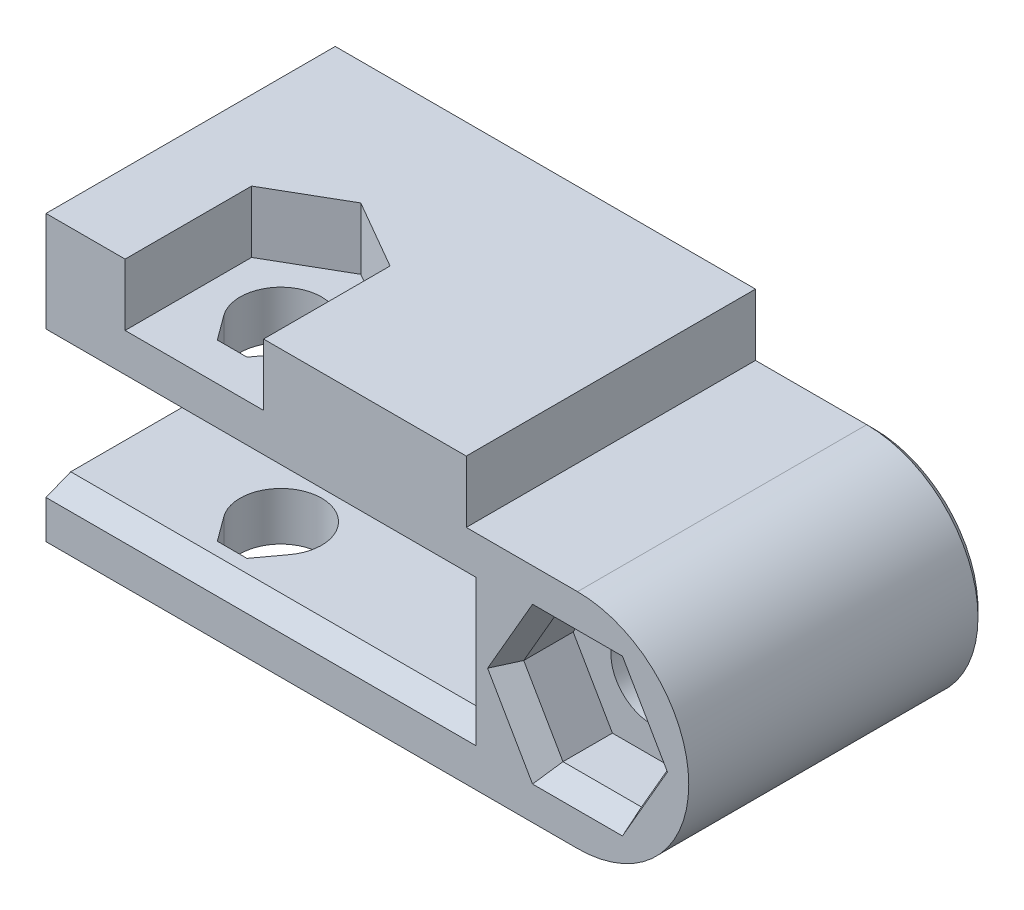
SolidWorks part; units mm, degrees
material "Custom Plastic"
ref_plane "Front Plane" through (0, 0, 0) normal (0, 0, 1) x (1, 0, 0)
ref_plane "Top Plane" through (0, 0, 0) normal (0, 1, 0) x (1, 0, 0)
ref_plane "Right Plane" through (0, 0, 0) normal (1, 0, 0) x (0, 0, -1)
sketch "Sketch1" plane through (0, 0, 0) normal (0, 0, 1) x (1, 0, 0)
  line L0 (-4, 7) -> (-4, -4.5)
  line L1 (22.5, 21.7711) -> (22.5, -13.7573) construction
  line L2 (-4, 0) -> (22.5, 0) construction
  line L3 (13, 4.5) -> (13, 7)
  line L4 (17.5, 4.5) -> (13, 4.5)
  line L5 (13, 7) -> (-4, 7)
  line L7 (-1.65, -1.65) -> (1.65, -1.65) construction
  line L14 (-1.65, 1.65) -> (1.65, 1.65) construction
  line L16 (17.5, -4.5) -> (-4, -4.5)
  circle A0 centre (17.5, 0) radius 1.65
  arc A1 (17.5, -4.5) -> (17.5, 4.5) centre (17.5, 0) ccw
  circle A2 centre (17.5, 0) radius 5 construction
  arc A6 (-1.65, 1.65) -> (-1.65, -1.65) centre (-1.65, 0) ccw construction
  circle A7 centre (0, 0) radius 1.65 construction
  arc A8 (1.65, -1.65) -> (1.65, 1.65) centre (1.65, 0) ccw construction
  dimension "D1" = 26.5
  dimension "D2" = 10
  dimension "D3" = 4.5
  dimension "D4" = 3.3
  dimension "D5" = 4
  dimension "D6" = 2.5
  dimension "D7" = 17
extrude "Boss-Extrude1" add sketch "Sketch1" along normal blind 12
sketch "Sketch2" plane through (0, 0, 12) normal (0, 0, 1) x (1, 0, 0)
  line L0 (-4, 7) -> (-4, -4.5) construction
  line L1 (13, -2.55) -> (-4, -2.55)
  line L2 (13, 2.55) -> (13, -2.55)
  line L3 (13, 2.55) -> (-4, 2.55)
  line L4 (-4, -2.55) -> (-4, 2.55)
  line L5 (13, -2.55) -> (-4, 2.55) construction
  line L6 (13, 2.55) -> (-4, -2.55) construction
  point P0 (4.5, 0)
  dimension "D1" = 5.1
  dimension "D2" = 17
extrude "Cut-Extrude1" cut sketch "Sketch2" against normal offset from surface (9 mm away) 3 up to face at (9.5833, 2.3333, 0)
sketch "Sketch3" plane through (0, 0, 12) normal (0, 0, 1) x (1, 0, 0)
  line L1 (14.3246, 0) -> (15.9123, -2.75)
  line L2 (15.9123, -2.75) -> (19.0877, -2.75)
  line L3 (19.0877, -2.75) -> (20.6754, 0)
  line L4 (20.6754, 0) -> (19.0877, 2.75)
  line L5 (19.0877, 2.75) -> (15.9123, 2.75)
  line L6 (15.9123, 2.75) -> (14.3246, 0)
  circle A0 centre (17.5, 0) radius 2.75 construction
  dimension "D1" = 5.5
extrude "Cut-Extrude2" cut sketch "Sketch3" against normal blind 3
chamfer "Chamfer1" distance 0.4 distance2 1 9 edges at (4.5, -2.55, 12) (13, 0, 12) (4.5, 2.55, 12) (15.1184, 1.375, 12) (17.5, 2.75, 12) (19.8816, 1.375, 12) (19.8816, -1.375, 12) (15.1184, -1.375, 12) (17.5, -2.75, 12)
chamfer "Chamfer2" distance 0.3 angle 45 7 edges at (-4, 1.25, 0) (6.75, -4.5, 0) (22, 0, 0) (15.25, 4.5, 0) (19.15, 0, 0) (13, 5.75, 0) (4.5, 7, 0)
sketch "Sketch4" plane through (0, -4.5, 0) normal (0, 1, 0) x (1, 0, 0)
  line L0 (-4, -3) -> (13, -3) construction
  line L1 (3.3295, -9.4771) -> (2.5999, -10.47)
  line L2 (2.5999, -10.47) -> (1.4001, -10.47)
  line L3 (1.4001, -10.47) -> (0.6705, -9.4771)
  line L4 (2, -10.47) -> (2, -10.15) construction
  line L5 (-4, -12) -> (-4, -0.3) construction
  arc A0 (3.3295, -9.4771) -> (0.6705, -9.4771) centre (2, -8.5) ccw
  dimension "D1" = 3.3
  dimension "D2" = 5.5
  dimension "D3" = 0.32
  dimension "D4" = 6
extrude "Cut-Extrude3" cut sketch "Sketch4" along normal through all
sketch "Sketch5" plane through (0, 7, 0) normal (0, 1, 0) x (1, 0, 0)
  line L0 (-0.8, -12) -> (4.8, -12)
  line L1 (4.8, -12) -> (4.8, -6.8834)
  line L2 (4.8, -6.8834) -> (2, -5.2668)
  line L3 (2, -5.2668) -> (-0.8, -6.8834)
  line L4 (-0.8, -6.8834) -> (-0.8, -12)
  line L5 (-0.6971, -10.176) -> (2, -11.7332) construction
  line L6 (2, -11.7332) -> (4.8529, -10.086) construction
  line L7 (13, -12) -> (-4, -12) construction
  circle A0 centre (2, -8.5) radius 2.8 construction
  dimension "D1" = 5.6
extrude "Cut-Extrude4" cut sketch "Sketch5" against normal blind 2.5
sketch "Sketch6" plane through (0, 0, 3) normal (0, 0, 1) x (1, 0, 0)
  line L0 (13, -2.55) -> (-4, -2.55) construction
  line L1 (-4, 2.55) -> (-2, 2.55)
  line L2 (-4, 2.55) -> (-4, -2.55)
  line L3 (-4, -2.55) -> (-2, -2.55)
  line L4 (-2, 2.55) -> (-2, -2.55)
  dimension "D1" = 2
extrude "Cut-Extrude5" cut sketch "Sketch6" against normal through all
equation "\"y-plate-thickness\"=5"
equation "\"bed-plate-thickness\"=6"
equation "\"x-plate-thickness\"=5"
equation "\"rod-diameter\"=12"
equation "\"D1@Sketch2\"=\"y-plate-thickness\"+0.1"
equation "\"y-cross-rib-thickness\"=6"
equation "\"y-rib-thickness\"=6"
equation "\"t-nut-hole-diameter\"=3"
equation "\"enclosure-thickness\"=0.6"
equation "\"M3-Clearance\"=3.3"
equation "\"M4-Clearance\"=4.3"
equation "\"M5-Clearance\"=5.3"
equation "\"M6-Clearance\"=6.3"
equation "\"M8-Clearance\"=8.3"
equation "\"623-Bearing-Dia\"=11.2"
